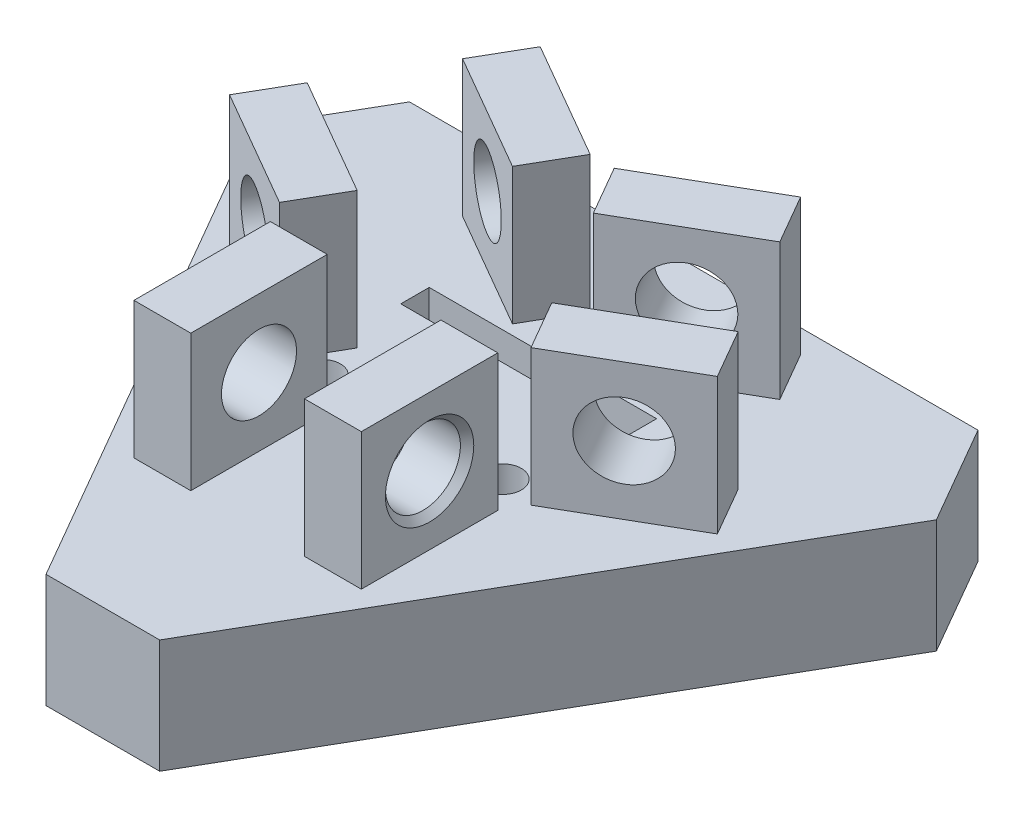
SolidWorks part; units mm, degrees
ref_plane "前视基准面" through (0, 0, 0) normal (0, 0, 1) x (1, 0, 0)
ref_plane "上视基准面" through (0, 0, 0) normal (0, 1, 0) x (1, 0, 0)
ref_plane "右视基准面" through (0, 0, 0) normal (1, 0, 0) x (0, 0, -1)
sketch "草图1" plane through (0, 0, 0) normal (0, 1, 0) x (1, 0, 0)
  line L0 (-32.8312, 24.6371) -> (17.1688, 24.6371)
  line L1 (17.1688, 24.6371) -> (22.1688, 15.9768)
  line L2 (22.1688, 15.9768) -> (-2.8312, -27.3245)
  line L3 (-2.8312, -27.3245) -> (-12.8312, -27.3245)
  line L4 (-12.8312, -27.3245) -> (-37.8312, 15.9768)
  line L5 (-32.8312, 24.6371) -> (-37.8312, 15.9768)
extrude "凸台-拉伸1" add sketch "草图1" along normal blind 10
sketch "草图2" plane through (0, 10, 0) normal (0, 1, 0) x (1, 0, 0)
  line L0 (-35.3312, 20.3069) -> (-7.8312, 4.4297) construction
  line L2 (-32.8312, 24.6371) -> (-37.8312, 15.9768) construction
  line L7 (-7.8312, 4.4297) -> (19.6688, 20.3069) construction
  line L8 (22.1688, 15.9768) -> (17.1688, 24.6371) construction
  line L14 (-7.8312, 4.4297) -> (-7.8312, -27.3245) construction
  line L15 (-12.8312, -27.3245) -> (-2.8312, -27.3245) construction
  line L20 (-8.8889, 16.5874) -> (-19.2812, 22.5874)
  line L21 (-8.8889, 16.5874) -> (-18.8889, -0.7331)
  line L24 (-19.2812, 22.5874) -> (-29.2812, 5.267)
  line L25 (-18.8889, -0.7331) -> (-29.2812, 5.267)
  line L30 (-8.8889, 16.5874) -> (-29.2812, 5.267) construction
  line L31 (-19.2812, 22.5874) -> (-18.8889, -0.7331) construction
  line L36 (13.6189, 5.267) -> (3.2266, -0.7331)
  line L37 (13.6189, 5.267) -> (3.6189, 22.5874)
  line L42 (3.2266, -0.7331) -> (-6.7734, 16.5874)
  line L43 (3.6189, 22.5874) -> (-6.7734, 16.5874)
  line L48 (13.6189, 5.267) -> (-6.7734, 16.5874) construction
  line L49 (3.2266, -0.7331) -> (3.6189, 22.5874) construction
  line L50 (2.1688, -14.5919) -> (2.1688, -2.5919)
  line L51 (2.1688, -14.5919) -> (-17.8312, -14.5919)
  line L52 (2.1688, -2.5919) -> (-17.8312, -2.5919)
  line L53 (-17.8312, -14.5919) -> (-17.8312, -2.5919)
  line L54 (2.1688, -14.5919) -> (-17.8312, -2.5919) construction
  line L55 (2.1688, -2.5919) -> (-17.8312, -14.5919) construction
  line L56 (-7.8312, -14.5919) -> (2.2937, -14.5919)
  line L57 (-17.8312, -14.5919) -> (-7.8312, -14.5919)
  line L58 (-17.8312, -2.5919) -> (-7.8312, -2.5919)
  line L59 (-7.8312, -2.5919) -> (2.1688, -2.5919)
  line L60 (-7.8312, -2.5919) -> (2.1688, -2.5919)
  line L61 (-2.8312, -2.5919) -> (-2.8312, -14.5919)
  line L62 (-17.8312, -14.5919) -> (-7.8312, -14.5919)
  line L63 (-12.8312, -14.5919) -> (-12.8312, -2.5919)
  line L64 (3.6189, 22.5874) -> (8.6189, 13.9272)
  line L65 (8.6189, 13.9272) -> (6.1189, 18.2573)
  line L66 (6.1189, 18.2573) -> (-4.2734, 12.2573)
  line L67 (3.2266, -0.7331) -> (-1.7734, 7.9272)
  line L68 (-1.7734, 7.9272) -> (0.7266, 3.5971)
  line L69 (0.7266, 3.5971) -> (11.1189, 9.5971)
  line L70 (-29.2812, 5.267) -> (-24.2812, 13.9272)
  line L71 (-24.2812, 13.9272) -> (-26.7812, 9.5971)
  line L72 (-26.7812, 9.5971) -> (-16.3889, 3.5971)
  line L73 (-24.2812, 13.9272) -> (-19.2812, 22.5874)
  line L74 (-21.7812, 18.2573) -> (-11.3889, 12.2573)
  circle A0 centre (-7.8312, 4.4297) radius 13 construction
  point P13 (-19.085, 10.9272)
  point P14 (3.4227, 10.9272)
  point P15 (-7.8312, -8.5919)
extrude "凸台-拉伸4" add sketch "草图2" along normal blind 12 contours L72 L70 L25 L21 | L24 L74 L21 L20 | L66 L64 L43 L42 | L69 L42 L36 L37 | L52 L61 L51 L50 | L62 L63 L58 L53
sketch "草图9" plane through (4.9603, 0, -8.5915) normal (0.5, 0, -0.866) x (-0.866, 0, -0.5)
  line L0 (21.9917, 10) -> (21.9917, 16)
  line L1 (15.9917, 10) -> (27.9917, 10) construction
hole_wizard "G1/16 螺纹孔1" positions "草图10" profile "草图11" tap size "G1/16" standard "GB"
sketch "草图10" plane through (4.9603, 0, -8.5915) normal (0.5, 0, -0.866) x (-0.866, 0, -0.5)
  point P0 (21.9917, 16)
sketch "草图11" plane through (-14.085, 16, -19.5874) normal (0, 1, 0) x (-0.866, 0, -0.5)
  line L0 (0, 0) -> (0, 51.9828)
  line L1 (0, 51.9828) -> (3.3, 50)
  line L2 (3.3, 50) -> (3.3, 0.5865)
  line L3 (3.3, 0.5865) -> (3.8865, 0)
  line L5 (3.8865, 0) -> (0, 0)
  line L6 (-3.3, 0.5865) -> (-3.8865, 0) construction
  line L10 (0, 51.9828) -> (-3.3, 50) construction
  line L11 (0, -6.35) -> (0, 107.95) construction
  dimension "螺纹孔钻头直径" = 6.6
  dimension "螺纹孔钻头深度" = 50
  dimension "近端锥形沉头孔直径" = 7.773
  dimension "近端锥形沉头孔角度" = 90
  dimension "导头角度" = 118
cosmetic thread "孔螺蚊线1" parameters "D1"=15.45, "D2"=7.723
sketch "草图12" plane through (-8.876, 0, -15.3735) normal (-0.5, 0, -0.866) x (-0.866, 0, 0.5)
  line L0 (-8.4278, 10) -> (-8.4278, 16)
  line L1 (-14.4278, 10) -> (-2.4278, 10) construction
hole_wizard "G1/16 螺纹孔2" positions "草图13" profile "草图14" tap size "G1/16" standard "GB"
sketch "草图13" plane through (-8.876, 0, -15.3735) normal (-0.5, 0, -0.866) x (-0.866, 0, 0.5)
  point P0 (-8.4278, 16)
sketch "草图14" plane through (-1.5773, 16, -19.5874) normal (0, 1, 0) x (-0.866, 0, 0.5)
  line L0 (0, 0) -> (0, 51.9828)
  line L1 (0, 51.9828) -> (3.3, 50)
  line L2 (3.3, 50) -> (3.3, 0.5865)
  line L3 (3.3, 0.5865) -> (3.8865, 0)
  line L5 (3.8865, 0) -> (0, 0)
  line L6 (-3.3, 0.5865) -> (-3.8865, 0) construction
  line L10 (0, 51.9828) -> (-3.3, 50) construction
  line L11 (0, -6.35) -> (0, 107.95) construction
  dimension "螺纹孔钻头直径" = 6.6
  dimension "螺纹孔钻头深度" = 50
  dimension "近端锥形沉头孔直径" = 7.773
  dimension "近端锥形沉头孔角度" = 90
  dimension "导头角度" = 118
cosmetic thread "孔螺蚊线2" parameters "D1"=15.45, "D2"=7.723
sketch "草图15" plane through (2.1688, 0, 0) normal (1, 0, 0) x (0, 0, -1)
  line L0 (-8.5919, 10) -> (-8.5919, 16)
  line L1 (-14.5919, 10) -> (-2.5919, 10) construction
hole_wizard "G1/16 螺纹孔3" positions "草图16" profile "草图17" tap size "G1/16" standard "GB"
sketch "草图16" plane through (2.1688, 0, 0) normal (1, 0, 0) x (0, 0, -1)
  point P0 (-8.5919, 16)
sketch "草图17" plane through (2.1688, 16, 8.5919) normal (0, 1, 0) x (0, 0, -1)
  line L0 (0, 0) -> (0, 51.9828)
  line L1 (0, 51.9828) -> (3.3, 50)
  line L2 (3.3, 50) -> (3.3, 0.5865)
  line L3 (3.3, 0.5865) -> (3.8865, 0)
  line L5 (3.8865, 0) -> (0, 0)
  line L6 (-3.3, 0.5865) -> (-3.8865, 0) construction
  line L10 (0, 51.9828) -> (-3.3, 50) construction
  line L11 (0, -6.35) -> (0, 107.95) construction
  dimension "螺纹孔钻头直径" = 6.6
  dimension "螺纹孔钻头深度" = 50
  dimension "近端锥形沉头孔直径" = 7.773
  dimension "近端锥形沉头孔角度" = 90
  dimension "导头角度" = 118
cosmetic thread "孔螺蚊线3" parameters "D1"=15.45, "D2"=7.723
sketch "草图18" plane through (0, 0, 0) normal (0, -1, 0) x (-1, 0, 0)
  line L0 (-17.1688, 24.6371) -> (-13.3775, 17.4073)
  line L1 (-13.3775, 17.4073) -> (-22.1688, 15.9768)
  line L2 (-13.3775, 0.7498) -> (0, 24.6371)
  line L3 (2.8312, -27.3245) -> (-22.1688, 15.9768) construction
  line L4 (-17.1688, 24.6371) -> (32.8312, 24.6371) construction
  line L5 (-13.3775, 0.7498) -> (-1.2378, -20.2769)
  line L6 (-1.2378, -20.2769) -> (36.5161, -12.1314)
  line L7 (-1.2378, -20.2769) -> (23.9153, 24.6371) construction
  line L8 (0, 24.6371) -> (23.9153, 24.6371)
  line L9 (23.9153, 24.6371) -> (36.5161, -12.1314)
  line M2 (32.8312, 24.6371) -> (-17.1688, 24.6371)
  line M4 (-22.1688, 15.9768) -> (2.8312, -27.3245)
  line M6 (12.8312, -27.3245) -> (37.8312, 15.9768)
extrude "凸台-拉伸5" add sketch "草图18" along normal blind 40 contours L9 L6 M6 | L7 L6 L9 M6 | L7 L2 M4 M2
sketch "草图19" plane through (-4.1251, 0, 19.1198) normal (-0.2109, 0, 0.9775) x (0.9775, 0, 0.2109)
  line L1 (-33.1362, 0) -> (16.8638, 0)
  line L2 (-33.1362, 0) -> (-33.1362, -30)
  line L3 (-33.1362, -30) -> (16.8638, -30)
  line L4 (16.8638, 0) -> (16.8638, -30)
extrude "切除-拉伸2" cut sketch "草图19" against normal blind 74
sketch "草图20" plane through (0, 0, 0) normal (0, -1, 0) x (1, 0, 0)
  line L0 (-12.8312, 27.3245) -> (-19.4809, 15.8068)
  line L1 (1.2378, 20.2769) -> (-36.5161, 12.1314) construction
  line L2 (-37.8312, -15.9768) -> (-12.8312, 27.3245) construction
  line L3 (-19.4809, 15.8068) -> (1.2378, 20.2769)
  line L4 (-2.8312, 27.3245) -> (22.1688, -15.9768) construction
  line L5 (1.2378, 20.2769) -> (-2.8312, 27.3245)
  line L6 (-2.8312, 27.3245) -> (-12.8312, 27.3245)
  line L7 (-37.8312, -15.9768) -> (-30.9611, -4.0776)
  line L8 (-23.9153, -24.6371) -> (-36.5161, 12.1314) construction
  line L9 (-30.9611, -4.0776) -> (-23.9153, -24.6371)
  line L10 (-23.9153, -24.6371) -> (-32.8312, -24.6371)
  line L11 (17.1688, -24.6371) -> (-32.8312, -24.6371) construction
  line L12 (-32.8312, -24.6371) -> (-37.8312, -15.9768) construction
  line L13 (-32.8312, -24.6371) -> (-37.8312, -15.9768)
extrude "凸台-拉伸6" add sketch "草图20" along normal blind 40
sketch "草图21" plane through (0, -40, 0) normal (0, -1, 0) x (-1, 0, 0)
  circle A0 centre (7.8312, 4.4298) radius 5.7735
sketch "草图23" plane through (0, -30, 0) normal (0, 1, 0) x (1, 0, 0)
  line L0 (-7.8312, 4.4298) -> (-7.8312, 24.6371) construction
  line L1 (-32.8312, 24.6371) -> (0, 24.6371) construction
  line L2 (-7.8312, 4.4298) -> (9.6688, -5.6738) construction
  line L3 (13.3775, 0.7498) -> (-2.8312, -27.3245) construction
  line L4 (-7.8312, 13.6674) -> (0.1688, -0.189)
  line L5 (-7.8312, 4.4298) -> (19.6688, 20.3069) construction
  line L6 (22.1688, 15.9768) -> (17.1688, 24.6371) construction
  circle A0 centre (0.1688, -0.189) radius 1.5
  circle A1 centre (-7.8312, 13.6674) radius 1.5
extrude "切除-拉伸3" cut sketch "草图23" against normal blind 6
sketch "草图24" plane through (0, 10, 0) normal (0, 1, 0) x (1, 0, 0)
  circle A0 centre (-7.8312, 4.4298) radius 5
sketch "草图25" plane through (-35.2915, 0, -20.3756) normal (-0.866, 0, -0.5) x (-0.5, 0, 0.866)
  line L1 (-9.3787, 0) -> (48.0607, 0)
  line L2 (-9.3787, 0) -> (-9.3787, -0.001)
  line L3 (-9.3787, -0.001) -> (48.0607, -0.001)
  line L4 (48.0607, 0) -> (48.0607, -0.001)
split "分割1" trim tools "草图25" bodies to split 113 resulting bodies 125 126 127 128
sketch "草图26" plane through (9.7085, 0, 5.6052) normal (0.866, 0, 0.5) x (0.5, 0, -0.866)
  line L5 (-48.0607, -0.001) -> (29.9913, -0.001)
  line L6 (-48.0607, -0.001) -> (-48.0607, -42.5903)
  line L7 (-48.0607, -42.5903) -> (29.9913, -42.5903)
  line L8 (29.9913, -0.001) -> (29.9913, -42.5903)
extrude "切除-拉伸5" cut sketch "草图26" against normal blind 147
hole_wizard "M4 螺纹孔1" positions "草图27" profile "草图28" tap size "M4" standard "GB"
sketch "草图27" plane through (0, 10, 0) normal (0, 1, 0) x (1, 0, 0)
  point P0 (-7.8312, 4.4298)
sketch "草图28" plane through (-7.8312, 10, -4.4298) normal (1, 0, 0) x (0, 0, 1)
  line L0 (0, 0) -> (0, 11.0914)
  line L1 (0, 11.0914) -> (1.65, 10.1)
  line L2 (1.65, 10.1) -> (1.65, 0)
  line L5 (1.65, 0) -> (0, 0)
  line L10 (0, 11.0914) -> (-1.65, 10.1) construction
  line L11 (0, -6.35) -> (0, 107.95) construction
  dimension "螺纹孔钻头直径" = 3.3
  dimension "螺纹孔钻头深度" = 10.1
  dimension "导头角度" = 118
cosmetic thread "孔螺蚊线4" parameters "D1"=8, "D2"=4
sketch "草图29" plane through (0, 0, 0) normal (0, -1, 0) x (-1, 0, 0)
  line L0 (7.8312, -1.3437) -> (12.8312, 7.3166)
  line L1 (12.8312, 7.3166) -> (2.8312, 7.3166)
  line L2 (2.8312, 7.3166) -> (7.8312, -1.3437)
  circle A0 centre (7.8312, 4.4298) radius 5.7735 construction
extrude "切除-拉伸6" cut sketch "草图29" against normal blind 4
ref_plane "基准面1" through (-2.8312, 0, -7.3166) normal (-0.5, 0, 0.866) x (0.866, 0, 0.5)
sketch "草图30" plane through (0, 0, 0) normal (0, -1, 0) x (-1, 0, 0)
  line L1 (17.8312, 11.3747) -> (-2.1688, 11.3747)
  line L2 (17.8312, 11.3747) -> (17.8312, 8.8747)
  line L3 (17.8312, 8.8747) -> (-2.1688, 8.8747)
  line L4 (-2.1688, 11.3747) -> (-2.1688, 8.8747)
extrude "切除-拉伸7" cut sketch "草图30" against normal blind 10
hole_wizard "M4 螺纹孔2" positions "草图31" profile "草图32" tap size "M4" standard "GB"
sketch "草图31" plane through (0, 0, 0) normal (0, -1, 0) x (-1, 0, 0)
  point P0 (0, 0)
  point P3 (15.9094, 0)
sketch "草图32" plane through (0, 0, 0) normal (1, 0, 0) x (0, 0, -1)
  line L0 (0, 0) -> (0, 11.0914)
  line L1 (0, 11.0914) -> (1.65, 10.1)
  line L2 (1.65, 10.1) -> (1.65, 0)
  line L5 (1.65, 0) -> (0, 0)
  line L10 (0, 11.0914) -> (-1.65, 10.1) construction
  line L11 (0, -6.35) -> (0, 107.95) construction
  dimension "螺纹孔钻头直径" = 3.3
  dimension "螺纹孔钻头深度" = 10.1
  dimension "导头角度" = 118
cosmetic thread "孔螺蚊线5" parameters "D1"=8, "D2"=4
cosmetic thread "孔螺蚊线6" parameters "D1"=8, "D2"=4
